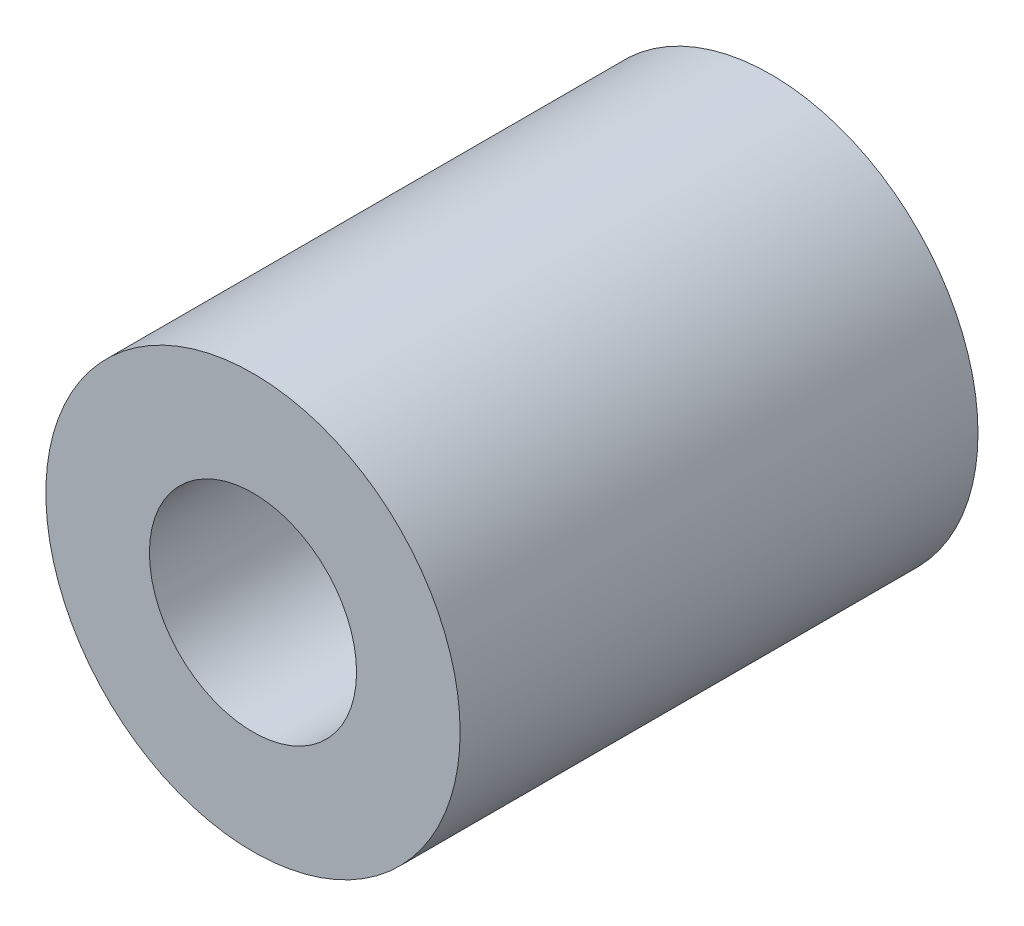
SolidWorks part; units mm, degrees
ref_plane "Front Plane" through (0, 0, 0) normal (0, 0, 1) x (1, 0, 0)
ref_plane "Top Plane" through (0, 0, 0) normal (0, 1, 0) x (1, 0, 0)
ref_plane "Right Plane" through (0, 0, 0) normal (1, 0, 0) x (0, 0, -1)
sketch "Sketch1" plane through (0, 0, 0) normal (0, 0, 1) x (1, 0, 0)
  circle A0 centre (0, 0) radius 10
  dimension "D1" = 20
extrude "Boss-Extrude1" add sketch "Sketch1" along normal mid plane 25
sketch "Sketch2" plane through (0, 0, 12.5) normal (0, 0, 1) x (1, 0, 0)
  circle A0 centre (0, 0) radius 5
  dimension "D1" = 10
extrude "Cut-Extrude2" cut sketch "Sketch2" against normal blind 8
mirror "Mirror1" about plane through (0, 0, 0) normal (0, 0, 1) of "Cut-Extrude2"
